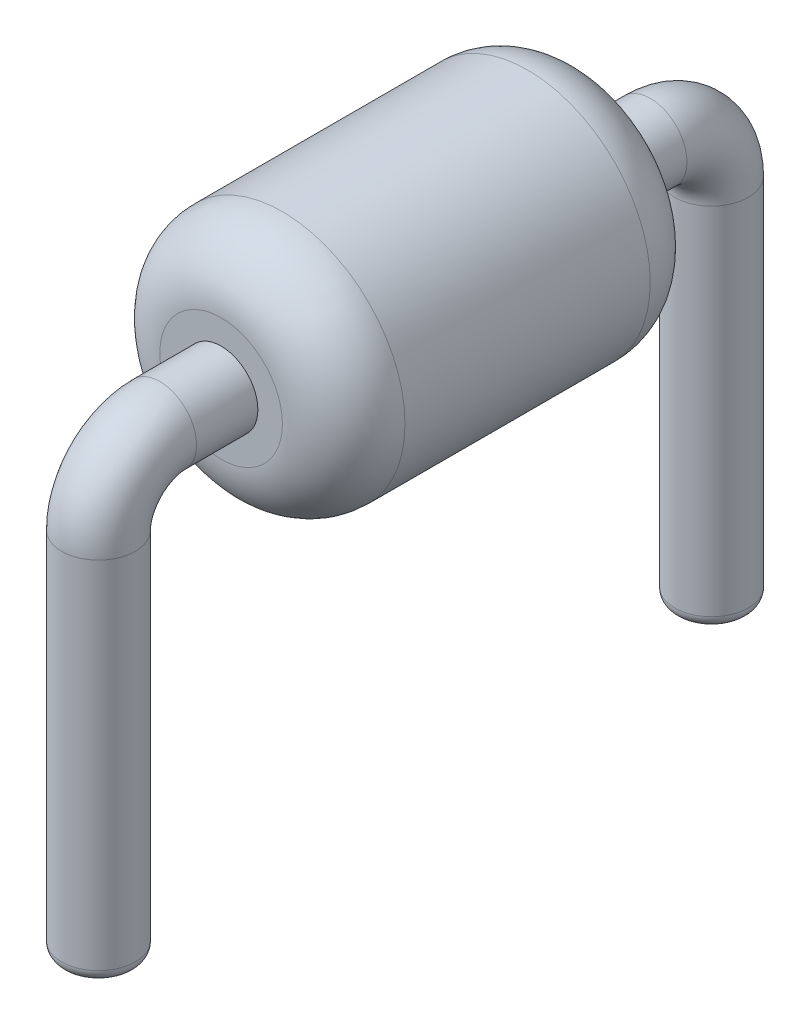
SolidWorks part; units mm, degrees
ref_plane "Ön Düzlem" through (0, 0, 0) normal (0, 0, 1) x (1, 0, 0)
ref_plane "Üst Düzlem" through (0, 0, 0) normal (0, 1, 0) x (1, 0, 0)
ref_plane "Sağ Düzlem" through (0, 0, 0) normal (1, 0, 0) x (0, 0, -1)
sketch "Sketch2" plane through (0, 0, 0) normal (1, 0, 0) x (0, 0, -1)
  line L0 (0, 0) -> (0, 3)
  line L1 (5, 0) -> (5, 3)
  line L2 (0.5, 3.5) -> (4.5, 3.5)
  line L3 (0, 3) -> (5, 3) construction
  line L4 (0, 0) -> (5, 0) construction
  arc A0 (0.5, 3.5) -> (0, 3) centre (0.5, 3) ccw
  arc A1 (5, 3) -> (4.5, 3.5) centre (4.5, 3) ccw
  dimension "D4" = 1
  dimension "D5" = 1
  dimension "D1" = 5
  dimension "D2" = 3
  dimension "D3" = 3
sketch "Sketch3" plane through (0, 0, 0) normal (0, 1, 0) x (1, 0, 0)
  circle A0 centre (0, 0) radius 0.3
  dimension "D1" = 0.6
sweep "Sweep1" add profiles "Sketch3" path "Sketch2"
ref_plane "Plane1" through (0, 0, -1) normal (0, 0, 1) x (1, 0, 0)
sketch "Sketch4" plane through (0, 0, -1) normal (0, 0, 1) x (1, 0, 0)
  circle A0 centre (0, 3.5) radius 0.3
  circle A1 centre (0, 3.5) radius 1
  dimension "D1" = 2
  dimension "D2" = 0.6
extrude "Boss-Extrude2" add sketch "Sketch4" against normal blind 3
fillet "Fillet1" radius 0.5 2 edges at (1, 3.5, -4) (1, 3.5, -1)
fillet "Fillet2" radius 0.1 2 edges at (0, 0, -5.3) (0, 0, 0.3)
